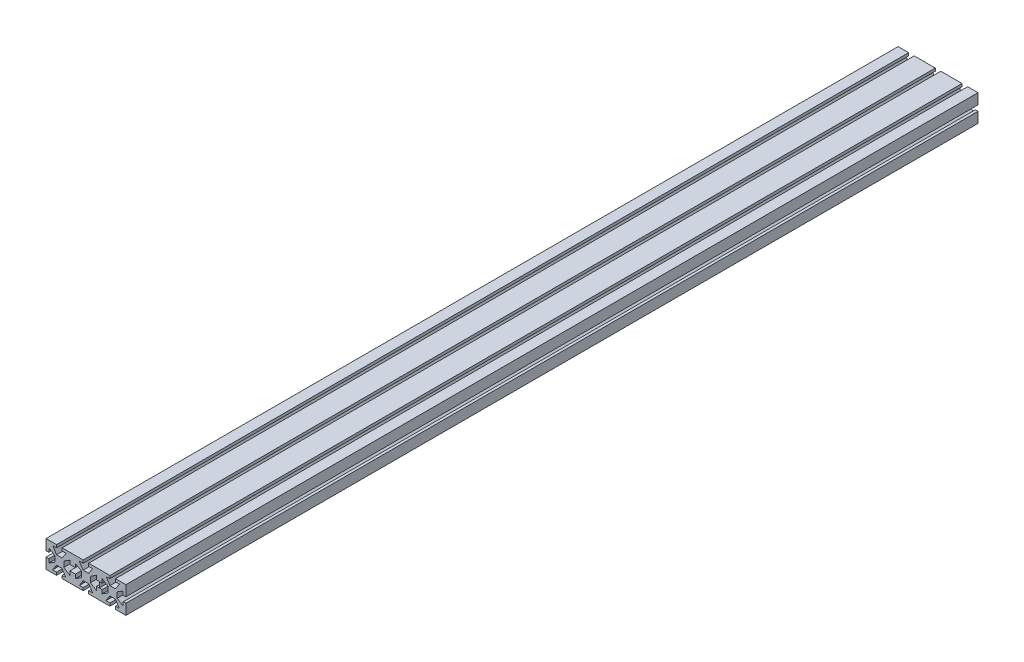
SolidWorks part; units mm, degrees
ref_plane "Front Plane" through (0, 0, 0) normal (0, 0, 1) x (1, 0, 0)
ref_plane "Top Plane" through (0, 0, 0) normal (0, 1, 0) x (1, 0, 0)
ref_plane "Right Plane" through (0, 0, 0) normal (1, 0, 0) x (0, 0, -1)
sketch "Sketch1" plane through (0, 0, 0) normal (0, 1, 0) x (1, 0, 0)
  line L1 (-57.15, -609.6) -> (57.15, -609.6)
  line L2 (-57.15, -609.6) -> (-57.15, 609.6)
  line L3 (-57.15, 609.6) -> (57.15, 609.6)
  line L4 (57.15, -609.6) -> (57.15, 609.6)
  line L5 (-57.15, -609.6) -> (57.15, 609.6) construction
  line L6 (-57.15, 609.6) -> (57.15, -609.6) construction
  point P0 (0, 0)
  dimension "D1" = 1219.2
  dimension "D2" = 114.3
extrude "Base Extrude" add sketch "Sketch1" along normal blind 38.1
sketch "Sketch3" plane through (0, 0, 609.6) normal (0, 0, 1) x (1, 0, 0)
  line L0 (-57.15, 38.1) -> (57.15, 38.1) construction
  line L1 (-42.0688, 38.1) -> (-34.1313, 38.1)
  line L2 (-42.0688, 38.1) -> (-42.0688, 34.1313)
  line L4 (-34.1313, 38.1) -> (-34.1313, 34.1313)
  line L5 (-57.15, 38.1) -> (-57.15, 0) construction
  line L6 (-47.3973, 34.1313) -> (-42.0688, 34.1313)
  line L7 (-28.3473, 34.1313) -> (-34.1313, 25.4953)
  line L8 (-34.1313, 25.4953) -> (-42.0688, 25.4953)
  line L9 (-42.0688, 25.4953) -> (-47.3973, 34.1313)
  line L10 (-34.1313, 34.1313) -> (-28.3473, 34.1313)
  line L11 (-23.0187, 28.3473) -> (-23.0187, 23.0188)
  line L12 (-31.6547, 23.0188) -> (-23.0187, 28.3473)
  line L13 (-31.6547, 15.0813) -> (-31.6547, 23.0188)
  line L14 (-23.0187, 9.2973) -> (-31.6547, 15.0813)
  line L15 (-23.0187, 15.0813) -> (-23.0187, 9.2973)
  line L16 (-19.05, 15.0813) -> (-23.0187, 15.0813)
  line L17 (-19.05, 23.0188) -> (-19.05, 15.0813)
  line L18 (-19.05, 23.0188) -> (-23.0187, 23.0188)
  line L19 (-28.8027, 3.9688) -> (-34.1312, 3.9688)
  line L20 (-34.1312, 12.6048) -> (-28.8027, 3.9688)
  line L21 (-42.0687, 12.6048) -> (-34.1312, 12.6048)
  line L22 (-47.8527, 3.9688) -> (-42.0687, 12.6048)
  line L23 (-42.0687, 3.9688) -> (-47.8527, 3.9688)
  line L24 (-42.0687, 0) -> (-42.0687, 3.9688)
  line L25 (-34.1312, 0) -> (-42.0687, 0)
  line L26 (-34.1312, 0) -> (-34.1312, 3.9688)
  line L27 (-53.1812, 9.7527) -> (-53.1812, 15.0812)
  line L28 (-44.5452, 15.0812) -> (-53.1812, 9.7527)
  line L29 (-44.5452, 23.0187) -> (-44.5452, 15.0812)
  line L30 (-53.1812, 28.8027) -> (-44.5452, 23.0187)
  line L31 (-53.1812, 23.0187) -> (-53.1812, 28.8027)
  line L32 (-57.15, 23.0187) -> (-53.1812, 23.0187)
  line L33 (-57.15, 15.0812) -> (-57.15, 23.0187)
  line L34 (-57.15, 15.0812) -> (-53.1812, 15.0812)
  dimension "D1" = 15.0812
  dimension "D2" = 7.9375
  dimension "D3" = 3.9688
  dimension "D4" = 19.05
  dimension "D5" = 4
extrude "Cut-Extrude1" cut sketch "Sketch3" against normal through all
ref_plane "Plane1" through (-19.05, 0, 0) normal (-1, 0, 0) x (0, 0, 1)
ref_plane "Plane2" through (19.1453, 0, 0) normal (1, 0, 0) x (0, 0, -1)
mirror "Mirror1" about plane through (-19.05, 0, 0) normal (-1, 0, 0) of "Cut-Extrude1"
mirror "Mirror2" about plane through (19.1453, 0, 0) normal (1, 0, 0) of "Mirror1"
